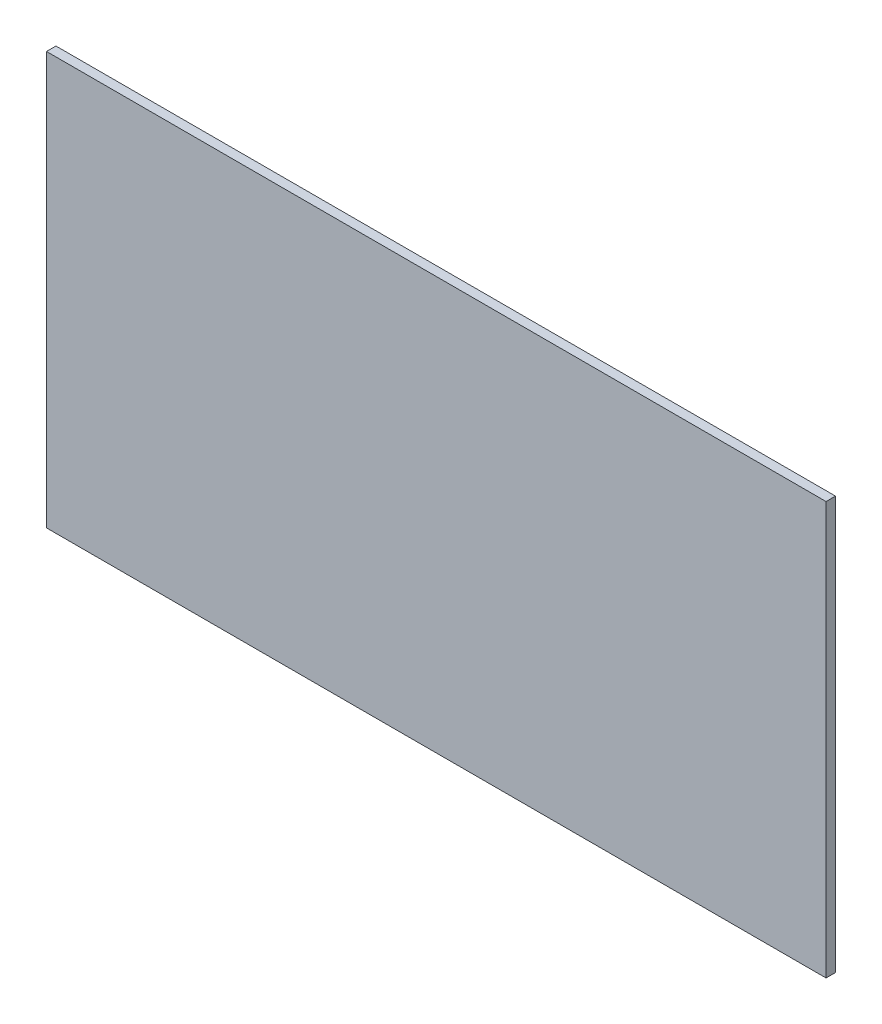
SolidWorks part; units mm, degrees
other "Câmera1"
ref_plane "Plano frontal" through (0, 0, 0) normal (0, 0, 1) x (1, 0, 0)
ref_plane "Plano superior" through (0, 0, 0) normal (0, 1, 0) x (1, 0, 0)
ref_plane "Plano direito" through (0, 0, 0) normal (1, 0, 0) x (0, 0, -1)
sketch "Esboço1" plane through (0, 0, 0) normal (0, 0, 1) x (1, 0, 0)
  line L1 (-33.2642, -7.425) -> (8.0158, -7.425)
  line L2 (-33.2642, -7.425) -> (-33.2642, 14.425)
  line L3 (-33.2642, 14.425) -> (8.0158, 14.425)
  line L4 (8.0158, -7.425) -> (8.0158, 14.425)
  line L5 (-33.2642, -7.425) -> (8.0158, 14.425) construction
  line L6 (-33.2642, 14.425) -> (8.0158, -7.425) construction
  point P0 (-12.6242, 3.5)
  dimension "D1" = 21.85
  dimension "D2" = 41.28
extrude "Ressalto-extrusão1" add sketch "Esboço1" along normal blind 0.5
